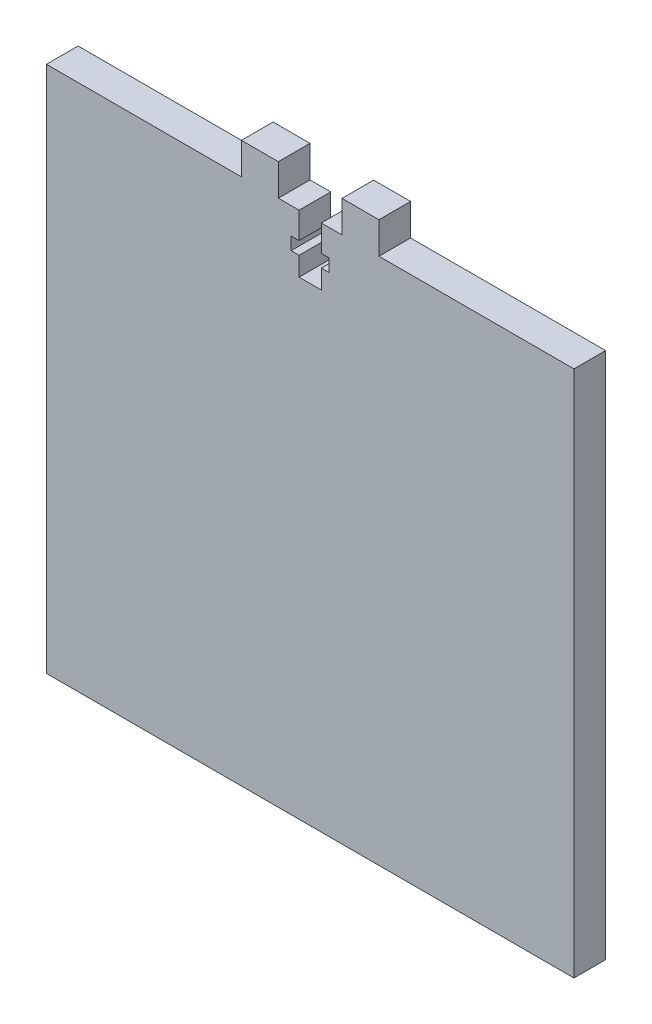
SolidWorks part; units mm, degrees
material "Клен"
ref_plane "Спереди" through (0, 0, 0) normal (0, 0, 1) x (1, 0, 0)
ref_plane "Сверху" through (0, 0, 0) normal (0, 1, 0) x (1, 0, 0)
ref_plane "Справа" through (0, 0, 0) normal (1, 0, 0) x (0, 0, -1)
sketch "Эскиз1" plane through (0, 0, 0) normal (0, 0, 1) x (1, 0, 0)
  line L1 (-50, -50) -> (50, -50)
  line L2 (-50, -50) -> (-50, 50)
  line L3 (-50, 50) -> (50, 50)
  line L4 (50, -50) -> (50, 50)
  line L5 (-50, -50) -> (50, 50) construction
  line L6 (-50, 50) -> (50, -50) construction
  point P0 (0, 0)
  dimension "D1" = 100
extrude "Бобышка-Вытянуть1" add sketch "Эскиз1" along normal blind 6
ref_plane "Плоскость1" through (0, 0, 3) normal (0, 0, 1) x (1, 0, 0)
sketch "Эскиз2" plane through (0, 0, 6) normal (0, 0, 1) x (1, 0, 0)
  line L0 (50, 50) -> (-50, 50) construction
  line L1 (-13.0318, 50) -> (-6.0318, 50)
  line L2 (-13.0318, 50) -> (-13.0318, 56)
  line L3 (-13.0318, 56) -> (-6.0318, 56)
  line L4 (-6.0318, 50) -> (-6.0318, 56)
  line L5 (13, 56) -> (-13, 56) construction
  line L6 (0, 53.4074) -> (0, -162.0434) construction
  line L7 (13.0318, 50) -> (6.0318, 50)
  line L8 (6.0318, 50) -> (6.0318, 56)
  line L9 (13.0318, 56) -> (6.0318, 56)
  line L10 (13.0318, 50) -> (13.0318, 56)
  dimension "D1" = 7
extrude "Бобышка-Вытянуть2" add sketch "Эскиз2" against normal blind 6
sketch "Эскиз3" plane through (0, 0, 6) normal (0, 0, 1) x (1, 0, 0)
  line L1 (6.0318, 50) -> (-6.0318, 50) construction
  line L3 (-2.1, 45) -> (-3.6, 45)
  line L4 (-3.6, 45) -> (-3.6, 42.6)
  line L5 (-3.6, 42.6) -> (-2.1, 42.6)
  line L8 (0, 53.4074) -> (0, -162.0434) construction
  line L11 (3.6, 42.6) -> (2.1, 42.6)
  line L12 (3.6, 45) -> (3.6, 42.6)
  line L13 (2.1, 45) -> (3.6, 45)
  line L16 (-2.1, 45) -> (-2.1, 50)
  line L17 (-2.1, 50) -> (2.1, 50)
  line L18 (2.1, 50) -> (2.1, 45)
  line L19 (2.1, 42.6) -> (2.1, 39)
  line L20 (2.1, 39) -> (-2.1, 39)
  line L21 (-2.1, 39) -> (-2.1, 42.6)
  line L23 (-13.0318, 50) -> (-50, 50) construction
  point P15 (0, 43.65)
  point P20 (0, 50)
  dimension "D1" = 5
  dimension "D2" = 7.2
  dimension "D3" = 2.4
  dimension "D4" = 4.2
  dimension "D5" = 11
extrude "Вырез-Вытянуть1" cut sketch "Эскиз3" against normal through all
